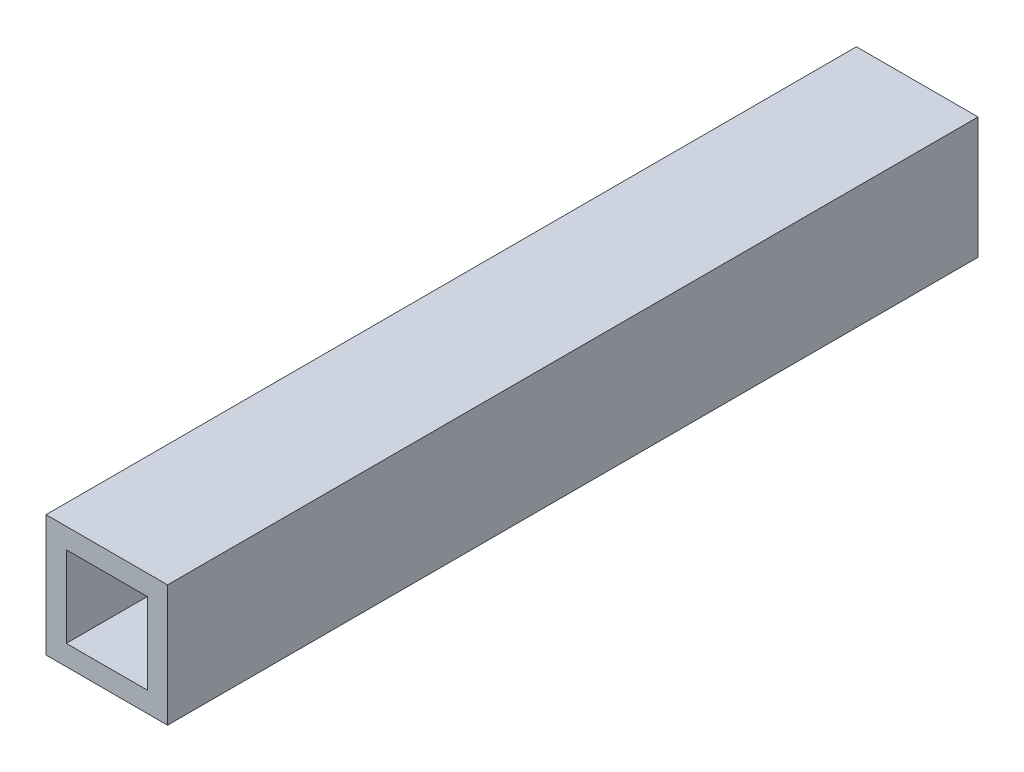
SolidWorks part; units mm, degrees
ref_plane "Front Plane" through (0, 0, 0) normal (0, 0, 1) x (1, 0, 0)
ref_plane "Top Plane" through (0, 0, 0) normal (0, 1, 0) x (1, 0, 0)
ref_plane "Right Plane" through (0, 0, 0) normal (1, 0, 0) x (0, 0, -1)
sketch "Sketch1" plane through (0, 0, 0) normal (0, 0, 1) x (1, 0, 0)
  line L1 (-9.525, -9.525) -> (9.525, -9.525)
  line L2 (-9.525, -9.525) -> (-9.525, 9.525)
  line L3 (-9.525, 9.525) -> (9.525, 9.525)
  line L4 (9.525, -9.525) -> (9.525, 9.525)
  line L5 (-9.525, -9.525) -> (9.525, 9.525) construction
  line L6 (-9.525, 9.525) -> (9.525, -9.525) construction
  point P0 (0, 0)
  dimension "D1" = 19.05
  dimension "D2" = 19.05
extrude "Boss-Extrude1" add sketch "Sketch1" against normal blind 127
sketch "Sketch2" plane through (0, 0, 0) normal (0, 0, 1) x (1, 0, 0)
  line L1 (-6.35, -6.35) -> (6.35, -6.35)
  line L2 (-6.35, -6.35) -> (-6.35, 6.35)
  line L3 (-6.35, 6.35) -> (6.35, 6.35)
  line L4 (6.35, -6.35) -> (6.35, 6.35)
  line L5 (-6.35, -6.35) -> (6.35, 6.35) construction
  line L6 (-6.35, 6.35) -> (6.35, -6.35) construction
  point P0 (0, 0)
  dimension "D1" = 12.7
  dimension "D2" = 12.7
extrude "Cut-Extrude1" cut sketch "Sketch2" against normal up to next
equation "\"D2@Sketch1\"=\"D1@Sketch1\""
equation "\"D2@Sketch2\"=\"D1@Sketch2\""
